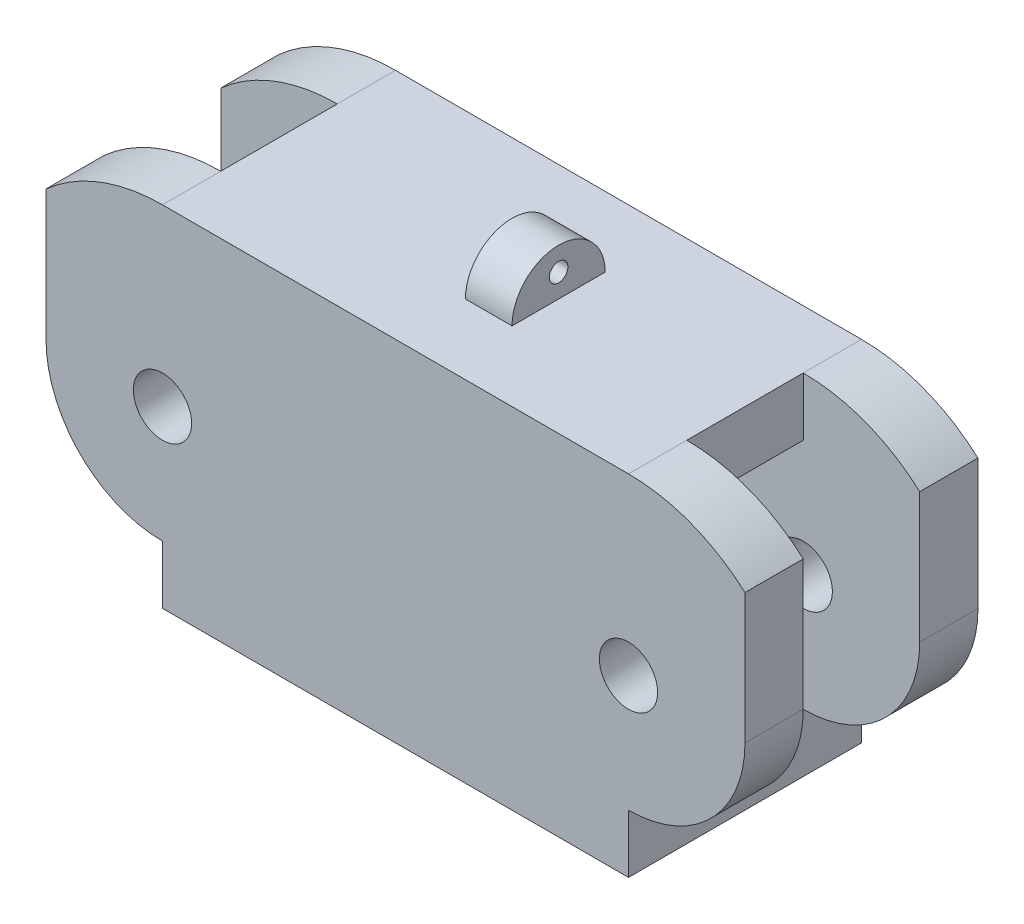
SolidWorks part; units mm, degrees
ref_plane "Front Plane" through (0, 0, 0) normal (0, 0, 1) x (1, 0, 0)
ref_plane "Top Plane" through (0, 0, 0) normal (0, 1, 0) x (1, 0, 0)
ref_plane "Right Plane" through (0, 0, 0) normal (1, 0, 0) x (0, 0, -1)
ref_plane "Right Side Plane" through (0, 0, 9.525) normal (0, 0, 1) x (1, 0, 0)
ref_plane "Inside Plane" through (0, 19.05, 0) normal (0, 1, 0) x (1, 0, 0)
sketch "Sketch1" plane through (0, 0, 0) normal (0, 1, 0) x (1, 0, 0)
  line L1 (-22.225, 9.525) -> (22.225, 9.525)
  line L2 (-22.225, 9.525) -> (-22.225, -9.525)
  line L3 (-22.225, -9.525) -> (22.225, -9.525)
  line L4 (22.225, 9.525) -> (22.225, -9.525)
  dimension "D1" = 19.05
  dimension "D2" = 44.45
  dimension "D3" = 22.225
  dimension "D4" = 9.525
extrude "Boss-Extrude1" add sketch "Sketch1" along normal blind 19.05
sketch "Sketch2" plane through (0, 0, 9.525) normal (0, 0, 1) x (1, 0, 0)
  line L2 (-22.225, 19.05) -> (22.225, 19.05) construction
  line L3 (-22.225, 19.05) -> (-22.225, 0) construction
  line L4 (-22.225, 0) -> (22.225, 0) construction
  line L5 (0, 0) -> (0, 19.05) construction
  circle A0 centre (-12.7, 9.525) radius 1.5875
  arc A1 (-12.7, 19.05) -> (-12.7, 0) centre (-12.7, 9.525) ccw
  arc A2 (-12.7, 19.05) -> (-12.7, 0) centre (-20.5633, 9.525) ccw
  arc A3 (12.7, 19.05) -> (12.7, 0) centre (20.5633, 9.525) cw
  arc A4 (12.7, 19.05) -> (12.7, 0) centre (12.7, 9.525) cw
  circle A5 centre (12.7, 9.525) radius 1.5875
extrude "Cut-Extrude1" cut sketch "Sketch2" against normal blind 19.05
sketch "Sketch9" plane through (0, 19.05, 0) normal (0, 1, 0) x (1, 0, 0)
  line L1 (0, -2.54) -> (2.54, -2.54)
  line L2 (0, -2.54) -> (0, 2.54)
  line L3 (0, 2.54) -> (2.54, 2.54)
  line L4 (2.54, -2.54) -> (2.54, 2.54)
  dimension "D1" = 5.08
  dimension "D2" = 2.54
  dimension "D3" = 0
  dimension "D4" = 2.54
extrude "Boss-Extrude2" add sketch "Sketch9" along normal blind 2.54
sketch "Sketch3" plane through (0, 0, 0) normal (1, 0, 0) x (0, 0, -1)
  line L0 (-9.525, 19.05) -> (-9.525, 0) construction
  line L1 (3.175, 15.875) -> (-3.175, 15.875)
  line L2 (3.175, 15.875) -> (3.175, 3.175)
  line L3 (3.175, 3.175) -> (-3.175, 3.175)
  line L4 (-3.175, 15.875) -> (-3.175, 3.175)
  line L5 (9.525, 19.05) -> (-9.525, 19.05) construction
  line L6 (9.525, 0) -> (9.525, 19.05) construction
  line L7 (9.525, 0) -> (-9.525, 0) construction
  line L8 (-2.54, 21.59) -> (2.54, 21.59) construction
  line L9 (-2.54, 21.59) -> (-2.54, 19.05) construction
  arc A0 (-2.54, 19.05) -> (2.54, 19.05) centre (0, 19.05) cw
  circle A1 centre (0, 20.32) radius 0.508
  arc A3 (-2.54, 19.05) -> (2.54, 19.05) centre (0, 20.9413) cw
  dimension "D5" = 1.27
  dimension "D1" = 6.35
  dimension "D2" = 3.175
  dimension "D3" = 6.35
  dimension "D4" = 3.175
  dimension "D6" = 2.54
extrude "Cut-Extrude2" cut sketch "Sketch3" against normal mid plane 76.2
sketch "Sketch4" plane through (0, 19.05, 0) normal (0, 1, 0) x (1, 0, 0)
  line L0 (-12.7, 9.525) -> (-12.7, -9.525) construction
  line L1 (-29.3612, -9.525) -> (-12.7, -9.525)
  line L2 (-29.3612, -9.525) -> (-29.3612, -6.35)
  line L3 (-29.3612, -6.35) -> (-12.7, -6.35)
  line L5 (12.7, 9.525) -> (12.7, -9.525) construction
  line L6 (-12.7, 6.35) -> (-31.5103, 6.35)
  line L8 (-11.1125, 9.525) -> (-31.5103, 9.525)
  line L9 (-31.5103, 6.35) -> (-31.5103, 9.525)
  line L10 (28.4066, -9.525) -> (1.5875, -9.525)
  line L11 (28.4066, -9.525) -> (28.4066, -6.35)
  line L12 (28.4066, -6.35) -> (1.5875, -6.35)
  line L14 (22.225, 9.525) -> (12.7, 9.525) construction
  line L15 (1.5875, 6.35) -> (30.675, 6.35)
  line L17 (1.5875, 9.525) -> (30.675, 9.525)
  line L18 (30.675, 6.35) -> (30.675, 9.525)
  line L20 (-12.7, 9.525) -> (-22.225, 9.525) construction
  line L22 (12.7, -3.175) -> (29.168, -3.175)
  line L23 (12.7, -3.175) -> (12.7, 3.175)
  line L24 (12.7, 3.175) -> (29.168, 3.175)
  line L25 (29.168, -3.175) -> (29.168, 3.175)
  line L30 (1.5875, -9.525) -> (-12.7, -9.525)
  line L31 (-12.7, -6.35) -> (1.5875, -6.35)
  line L32 (1.5875, 6.35) -> (-12.7, 6.35)
  line L33 (-11.1125, 9.525) -> (1.5875, 9.525)
  dimension "D1" = 3.175
  dimension "D2" = 3.175
  dimension "D5" = 3.175
  dimension "D6" = 3.175
extrude "Cut-Extrude3" cut sketch "Sketch4" against normal blind 43.18
sketch "Sketch6" plane through (0, 0, 9.525) normal (0, 0, 1) x (1, 0, 0)
  line L1 (12.7, 0) -> (31.9801, 0)
  line L2 (12.7, 0) -> (12.7, 3.175)
  line L4 (31.9801, 0) -> (31.9801, 3.175)
  line L6 (19.05, 9.525) -> (19.05, 19.7557)
  line L7 (19.05, 19.7557) -> (26.1322, 13.8085)
  line L8 (26.1322, 13.8085) -> (31.9801, 3.175)
  line L9 (22.225, 9.525) -> (19.05, 9.525) construction
  line L10 (-12.7, 0) -> (-12.7, 3.175)
  line L13 (-19.05, 9.525) -> (-19.05, 20.9428)
  line L14 (-19.05, 20.9428) -> (-28.9216, 11.7677)
  line L15 (-28.9216, 11.7677) -> (-28.9216, 0)
  line L16 (-28.9216, 0) -> (-12.7, 0)
  arc A1 (19.05, 9.525) -> (12.7, 3.175) centre (12.7, 9.525) cw
  arc A2 (12.7, 0) -> (12.7, 19.05) centre (12.7, 9.525) ccw construction
  arc A3 (-12.7, 3.175) -> (-19.05, 9.525) centre (-12.7, 9.525) cw
  arc A4 (-12.7, 19.05) -> (-12.7, 0) centre (-12.7, 9.525) ccw construction
  point P5 (20.1014, 9.2775)
  point P21 (-22.225, 9.525)
  point P23 (22.225, 9.525)
  point P27 (22.225, 9.525)
  dimension "D5" = 3.175
  dimension "D1" = 3.175
  dimension "D2" = 3.175
  dimension "D3" = 3.175
  dimension "D4" = 3.175
extrude "Cut-Extrude4" cut sketch "Sketch6" against normal blind 19.05
sketch "Sketch7" plane through (0, 19.05, 0) normal (0, 1, 0) x (1, 0, 0)
  line L0 (-12.7, 6.35) -> (-12.7, -6.35) construction
  line L1 (-27.7489, -3.175) -> (-12.7, -3.175)
  line L2 (-27.7489, -3.175) -> (-27.7489, 3.175)
  line L3 (-27.7489, 3.175) -> (-12.7, 3.175)
  line L4 (-12.7, -3.175) -> (-12.7, 3.175)
  line L5 (-19.05, -6.35) -> (-12.7, -6.35) construction
  line L6 (-12.7, 6.35) -> (-19.05, 6.35) construction
  dimension "D1" = 0
  dimension "D2" = 3.175
  dimension "D3" = 3.175
extrude "Cut-Extrude5" cut sketch "Sketch7" against normal blind 3.81
